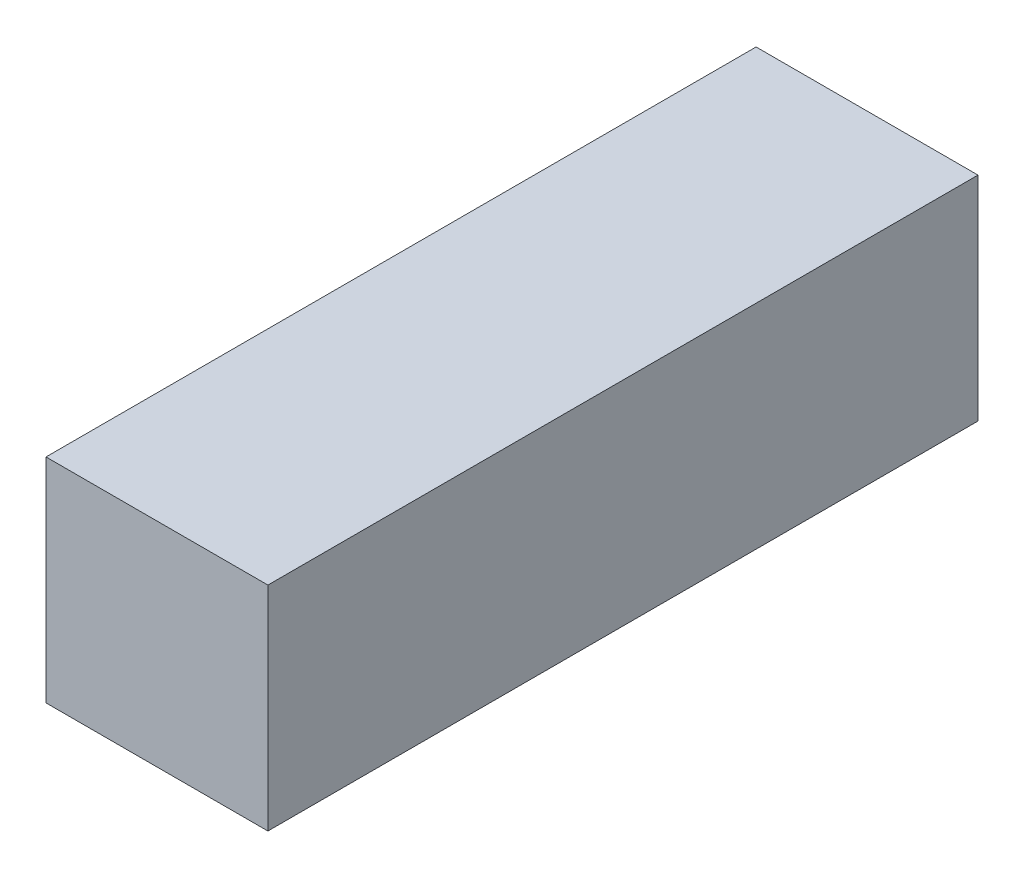
SolidWorks part; units mm, degrees
ref_plane "Piano frontale" through (0, 0, 0) normal (0, 0, 1) x (1, 0, 0)
ref_plane "Piano superiore" through (0, 0, 0) normal (0, 1, 0) x (1, 0, 0)
ref_plane "Piano destro" through (0, 0, 0) normal (1, 0, 0) x (0, 0, -1)
sketch "Schizzo1" plane through (0, 2575.799, 0) normal (0, -1, 0) x (-1, 0, 0)
  line L0 (379.1617, -2730.3029) -> (379.1617, -2744.1108) construction
  line L1 (354.1617, -2657.2069) -> (404.1617, -2657.2069)
  line L2 (354.1617, -2657.2069) -> (354.1617, -2817.2069)
  line L3 (354.1617, -2817.2069) -> (404.1617, -2817.2069)
  line L4 (404.1617, -2657.2069) -> (404.1617, -2817.2069)
  line L5 (354.1617, -2657.2069) -> (404.1617, -2817.2069) construction
  line L6 (354.1617, -2817.2069) -> (404.1617, -2657.2069) construction
  point P0 (379.1617, -2737.2069)
  dimension "D1" = 50
  dimension "D2" = 160
extrude "Estrusione-Estrusione1" add sketch "Schizzo1" along normal blind 48
ref_point "Punto1"
ref_plane "Piano1" through (0, 0, 2737.2069) normal (0, 0, 1) x (1, 0, 0)
